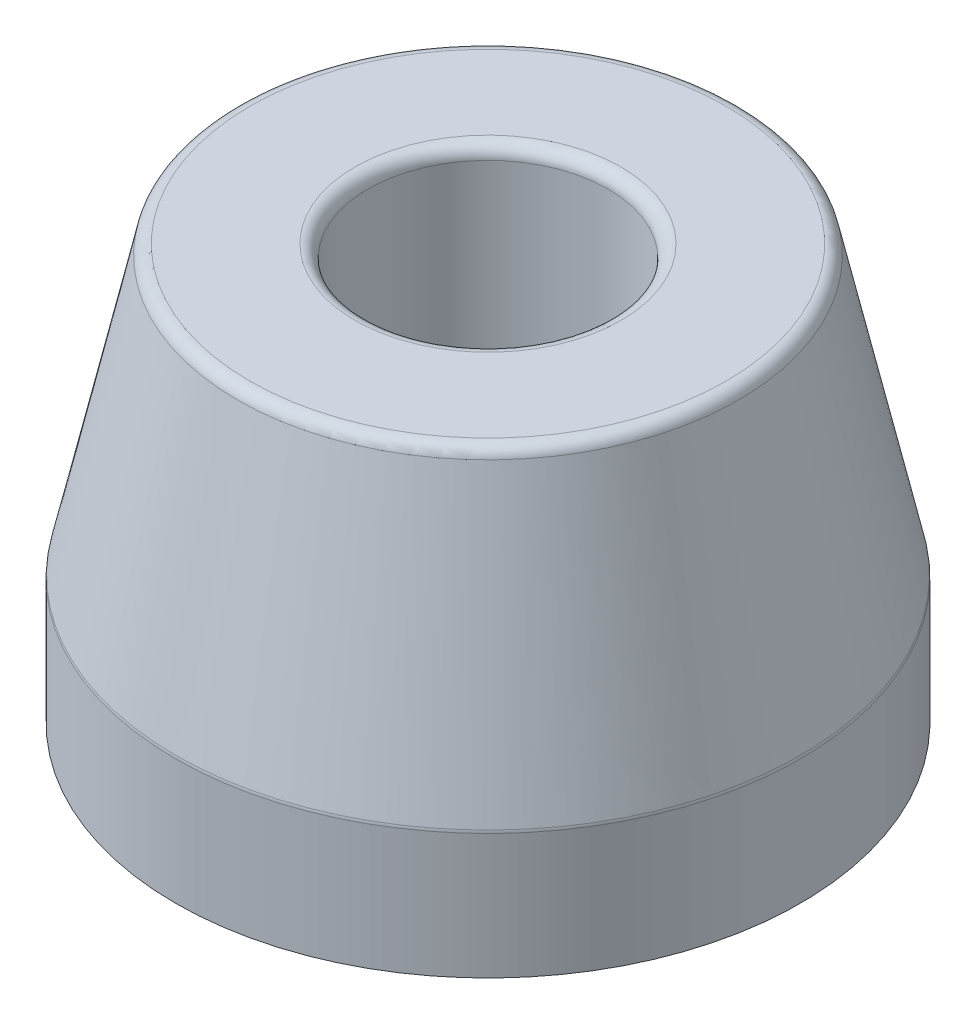
SolidWorks part; units mm, degrees
material "POLYURETHANE (11671)"
ref_plane "Front" through (0, 0, 0) normal (0, 0, 1) x (1, 0, 0)
ref_plane "Top" through (0, 0, 0) normal (0, 1, 0) x (1, 0, 0)
ref_plane "Right" through (0, 0, 0) normal (1, 0, 0) x (0, 0, -1)
sketch "Sketch1" plane through (0, 0, 0) normal (0, 0, 1) x (1, 0, 0)
  line L0 (4.7625, 0) -> (4.7625, 15.937)
  line L1 (5.2705, 16.445) -> (9.435, 16.445)
  line L2 (9.9309, 16.0472) -> (12.3704, 5.0694)
  line L3 (12.3825, 4.9592) -> (12.3825, 0)
  line L4 (12.3825, 0) -> (4.7625, 0)
  line L5 (0, 0) -> (0, 16.445) construction
  arc A0 (12.3704, 5.0694) -> (12.3825, 4.9592) centre (11.8745, 4.9592) cw
  arc A1 (4.7625, 15.937) -> (5.2705, 16.445) centre (5.2705, 15.937) cw
  arc A2 (9.435, 16.445) -> (9.9309, 16.0472) centre (9.435, 15.937) cw
  point P8 (12.3825, 5.015)
  point P11 (4.7625, 16.445)
  point P14 (9.8425, 16.445)
  dimension "D6" = 0.508
  dimension "D1" = 16.445
  dimension "D2" = 4.7625
  dimension "D3" = 5.08
  dimension "D4" = 5.015
  dimension "D5" = 7.62
revolve "Revolve1" add sketch "Sketch1" angle 360 about L5
